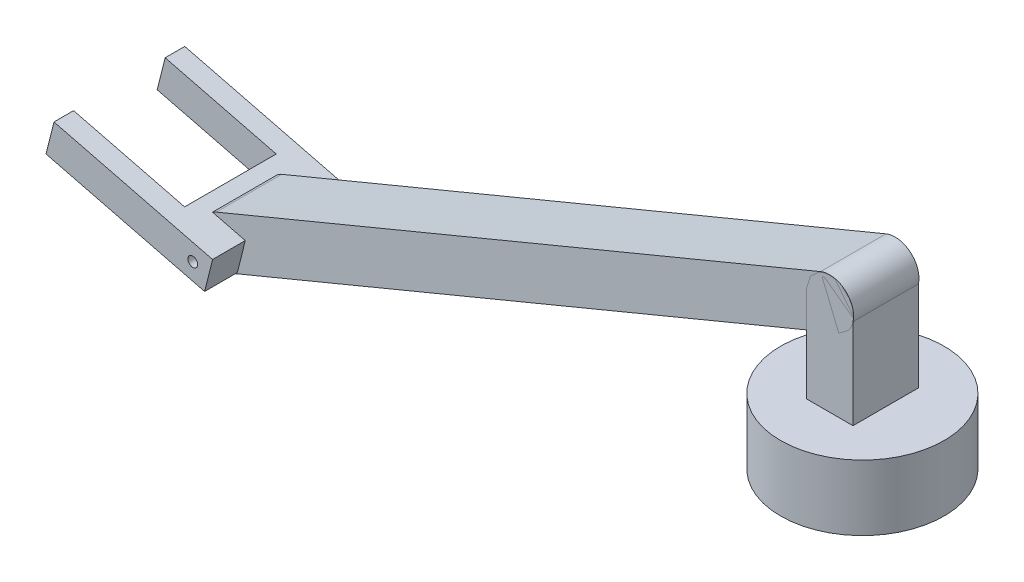
SolidWorks part; units mm, degrees
ref_plane "前基準面" through (0, 0, 0) normal (0, 0, 1) x (1, 0, 0)
ref_plane "上基準面" through (0, 0, 0) normal (0, 1, 0) x (1, 0, 0)
ref_plane "右基準面" through (0, 0, 0) normal (1, 0, 0) x (0, 0, -1)
sketch "草圖2" plane through (0, 0, 0) normal (0, 1, 0) x (1, 0, 0)
  circle A0 centre (0, 0) radius 25
  dimension "D1" = 50
extrude "填料-伸長1" add sketch "草圖2" along normal blind 20
sketch "草圖4" plane through (0, 0, 0) normal (0, 0, 1) x (1, 0, 0)
  line L0 (0, 20) -> (0, 49.1014) construction
  line L1 (-7.1256, 20) -> (-7.1256, 49.1014)
  line L2 (7.1256, 20) -> (7.1256, 49.1014)
  line L3 (25, 20) -> (-25, 20) construction
  arc A0 (-7.1256, 20) -> (7.1256, 20) centre (0, 20) ccw
  arc A1 (7.1256, 49.1014) -> (-7.1256, 49.1014) centre (0, 49.1014) ccw
  point P2 (0, 34.5507)
extrude "填料-伸長2" add sketch "草圖4" along normal mid plane 20
sketch "草圖5" plane through (0, 0, 0) normal (0, 0, 1) x (1, 0, 0)
  line L0 (0, 49.1014) -> (-184.7435, -27.5135) construction
  line L1 (2.7972, 42.3564) -> (-181.9463, -34.2584)
  line L2 (-2.7972, 55.8463) -> (-187.5407, -20.7685)
  arc A0 (2.7972, 42.3564) -> (-2.7972, 55.8463) centre (0, 49.1014) ccw
  arc A1 (-187.5407, -20.7685) -> (-181.9463, -34.2584) centre (-184.7435, -27.5135) ccw
  point P3 (-92.3718, 10.7939)
  dimension "D1" = 200
extrude "填料-伸長3" add sketch "草圖5" along normal mid plane 20 separate body
sketch "草圖6" plane through (0, 0, 0) normal (0, 0, 1) x (1, 0, 0)
  line L0 (-181.1096, -33.5794) -> (-178.6776, -23.8796)
  line L1 (-181.1096, -33.5794) -> (-229.6084, -21.4194)
  line L2 (-178.6776, -23.8796) -> (-227.1764, -11.7196)
  line L3 (-229.6084, -21.4194) -> (-227.1764, -11.7196)
  line L4 (-184.7435, -27.5135) -> (-179.8936, -28.7295) construction
  circle A0 centre (-184.7435, -27.5135) radius 1.5
  arc A1 (-187.5407, -20.7685) -> (-181.9463, -34.2584) centre (-184.7435, -27.5135) ccw construction
  dimension "D4" = 3
  dimension "D1" = 50
  dimension "D2" = 10
  dimension "D3" = 5
extrude "填料-伸長4" add sketch "草圖6" along normal mid plane 60
sketch "草圖7" plane through (-16.2013, -64.617, 0) normal (0.2432, 0.97, 0) x (0.97, -0.2432, 0)
  line L0 (-217.5055, -30) -> (-217.5055, 30) construction
  line L1 (-217.5055, 14) -> (-182.5055, 14)
  line L2 (-217.5055, 14) -> (-217.5055, -14)
  line L3 (-217.5055, -14) -> (-182.5055, -14)
  line L4 (-182.5055, 14) -> (-182.5055, -14)
  line L5 (-167.5055, 30) -> (-217.5055, 30) construction
  line L6 (-167.5055, -30) -> (-217.5055, -30) construction
  line L7 (-167.5055, 10) -> (-167.5055, 30) construction
  line L9 (-217.5055, 30) -> (-134.5505, 30)
  line L10 (-217.5055, 30) -> (-217.5055, 20)
  line L11 (-217.5055, 20) -> (-134.5505, 20)
  line L12 (-134.5505, 30) -> (-134.5505, 20)
  line L13 (-217.5055, -30) -> (-134.5505, -30)
  line L14 (-217.5055, -30) -> (-217.5055, -20)
  line L15 (-217.5055, -20) -> (-134.5505, -20)
  line L16 (-134.5505, -30) -> (-134.5505, -20)
  dimension "D1" = 16
  dimension "D2" = 16
  dimension "D3" = 15
  dimension "D4" = 10
  dimension "D5" = 10
extrude "除料-伸長1" cut sketch "草圖7" against normal through all
